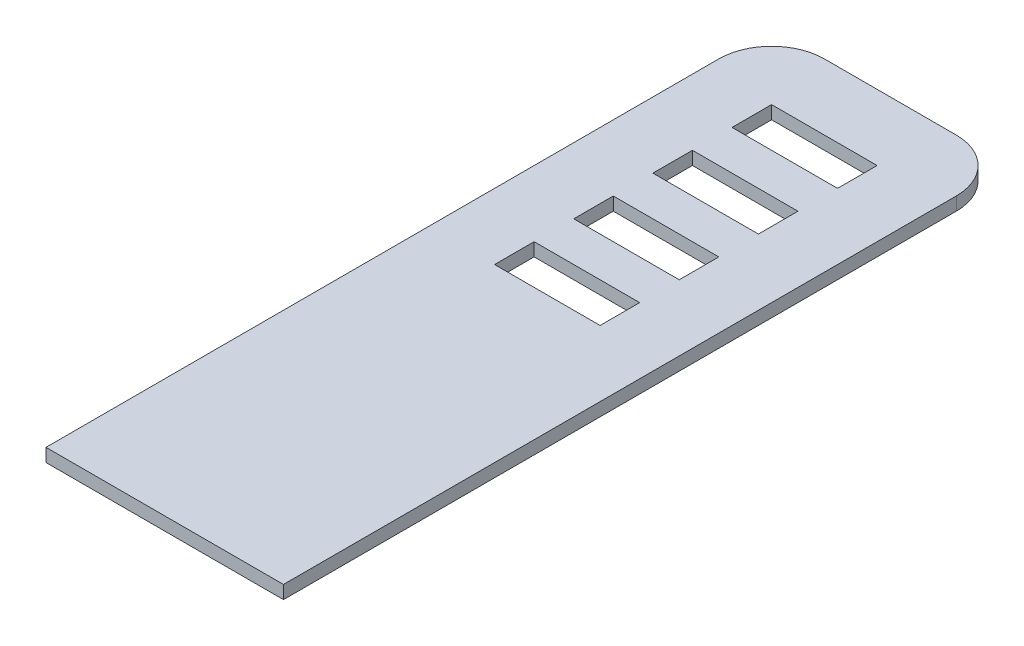
SolidWorks part; units mm, degrees
ref_plane "Front Plane" through (0, 0, 0) normal (0, 0, 1) x (1, 0, 0)
ref_plane "Top Plane" through (0, 0, 0) normal (0, 1, 0) x (1, 0, 0)
ref_plane "Right Plane" through (0, 0, 0) normal (1, 0, 0) x (0, 0, -1)
sketch "Sketch1" plane through (0, 0, 0) normal (0, 1, 0) x (1, 0, 0)
  line L11 (0, -55) -> (18, -55)
  line L18 (0, 0) -> (0, -55)
  line L19 (18, 0) -> (18, -55)
  line L26 (18, 0) -> (0, 0)
  dimension "D1" = 18
  dimension "D2" = 55
extrude "Boss-Extrude1" add sketch "Sketch1" along normal blind 1
sketch "Sketch2" plane through (0, 0, 0) normal (0, -1, 0) x (1, 0, 0)
  line L0 (9, 55) -> (9, 39.6) construction
  line L1 (0, 55) -> (18, 55) construction
  line L2 (5.2, 50.8) -> (12.8, 50.8)
  line L3 (5, 51) -> (13, 51) construction
  line L4 (5, 51) -> (5, 47) construction
  line L5 (5, 47) -> (13, 47) construction
  line L6 (13, 51) -> (13, 47) construction
  line L7 (5, 51) -> (13, 47) construction
  line L8 (5, 47) -> (13, 51) construction
  line L9 (5, 41.6) -> (13, 41.6) construction
  line L10 (5, 41.6) -> (5, 37.6) construction
  line L11 (5, 37.6) -> (13, 37.6) construction
  line L12 (13, 41.6) -> (13, 37.6) construction
  line L13 (5, 41.6) -> (13, 37.6) construction
  line L14 (5, 37.6) -> (13, 41.6) construction
  line L15 (12.8, 50.8) -> (12.8, 47.2)
  line L16 (5.2, 47.2) -> (12.8, 47.2)
  line L17 (5.2, 50.8) -> (5.2, 47.2)
  line L18 (12.8, 41.4) -> (12.8, 37.8)
  line L19 (5.2, 37.8) -> (12.8, 37.8)
  line L20 (5.2, 41.4) -> (5.2, 37.8)
  line L21 (5.2, 41.4) -> (12.8, 41.4)
  point P4 (9, 49)
  dimension "D1" = 4
  dimension "D2" = 8
  dimension "D3" = 4
  dimension "D4" = 5.4
  dimension "D5" = 0.2
  dimension "D6" = 0.2
extrude "Boss-Extrude2" add sketch "Sketch2" along normal blind 1
sketch "Sketch3" plane through (0, 0, 0) normal (0, -1, 0) x (1, 0, 0)
  line L0 (9, 0) -> (9, 6.5) construction
  line L1 (18, 0) -> (0, 0) construction
  line L2 (5, 14) -> (13, 14)
  line L3 (5, 8) -> (13, 8)
  line L4 (5, 8) -> (5, 5)
  line L5 (5, 5) -> (13, 5)
  line L6 (13, 8) -> (13, 5)
  line L7 (5, 8) -> (13, 5) construction
  line L8 (5, 5) -> (13, 8) construction
  line L9 (5, 14) -> (5, 11)
  line L10 (5, 11) -> (13, 11)
  line L11 (13, 14) -> (13, 11)
  line L12 (5, 14) -> (13, 11) construction
  line L13 (5, 11) -> (13, 14) construction
  line L14 (5, 20) -> (13, 20)
  line L15 (5, 20) -> (5, 17)
  line L16 (5, 17) -> (13, 17)
  line L17 (13, 20) -> (13, 17)
  line L18 (5, 20) -> (13, 17) construction
  line L19 (5, 17) -> (13, 20) construction
  line L20 (5, 26) -> (13, 26)
  line L21 (5, 26) -> (5, 23)
  line L22 (5, 23) -> (13, 23)
  line L23 (13, 26) -> (13, 23)
  line L24 (5, 26) -> (13, 23) construction
  line L25 (5, 23) -> (13, 26) construction
  point P10 (9, 4.5)
  dimension "D1" = 3
  dimension "D2" = 8
  dimension "D3" = 5
  dimension "D5" = 3
  dimension "D4" = 4
extrude "Cut-Extrude1" cut sketch "Sketch3" against normal through all
fillet "Fillet1" radius 4 2 edges at (0, 0.5, 0) (18, 0.5, 0)
